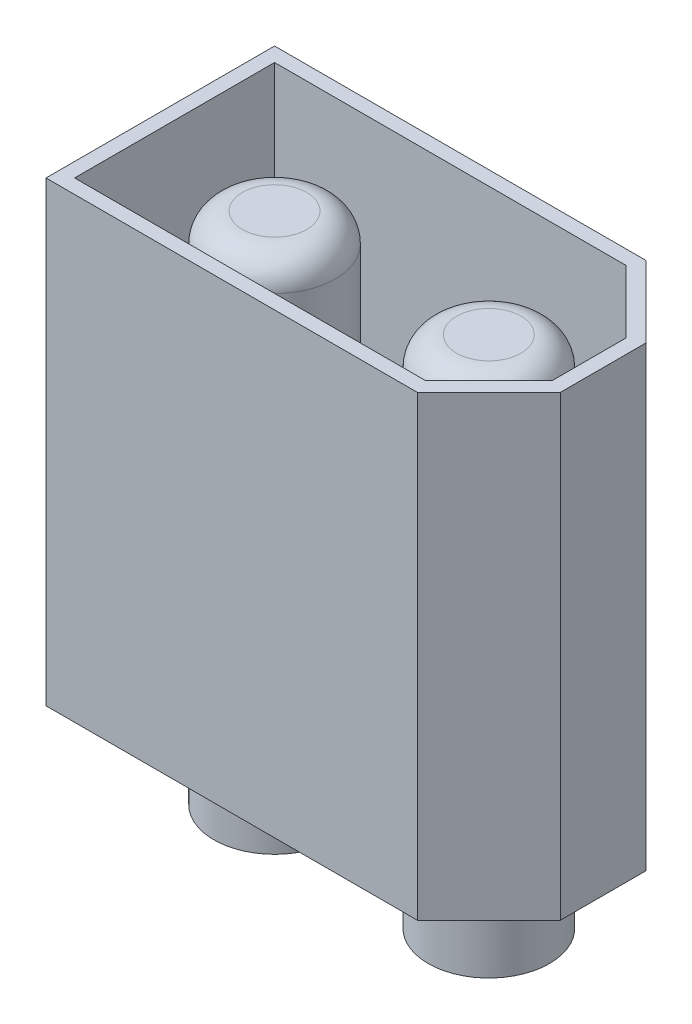
SolidWorks part; units mm, degrees
ref_plane "Front Plane" through (0, 0, 0) normal (0, 0, 1) x (1, 0, 0)
ref_plane "Top Plane" through (0, 0, 0) normal (0, 1, 0) x (1, 0, 0)
ref_plane "Right Plane" through (0, 0, 0) normal (1, 0, 0) x (0, 0, -1)
sketch "Sketch1" plane through (0, 0, 0) normal (0, 1, 0) x (1, 0, 0)
  line L0 (5.25, 4) -> (7.75, 1.5)
  line L1 (-7.75, 4) -> (7.75, 4)
  line L2 (-7.75, 4) -> (-7.75, -4)
  line L3 (-7.75, -4) -> (7.75, -4)
  line L4 (7.75, 4) -> (7.75, -4)
  line L5 (-7.75, 4) -> (7.75, -4) construction
  line L6 (-7.75, -4) -> (7.75, 4) construction
  line L7 (0, 0) -> (7.75, 0) construction
  line L8 (5.25, -4) -> (7.75, -1.5)
  point P0 (0, 0)
  dimension "D1" = 8
  dimension "D2" = 15.5
  dimension "D3" = 13
  dimension "D4" = 1.5
extrude "Boss-Extrude1" add sketch "Sketch1" along normal blind 16 contours L3 L8 L4 L0 L1 L2
shell "Shell1" thickness 0.5
sketch "Sketch2" plane through (0, 0, 0) normal (0, -1, 0) x (1, 0, 0)
  line L0 (0, 0) -> (0, 4) construction
  line L1 (-7.75, 4) -> (5.25, 4) construction
  circle A0 centre (-3.75, 0) radius 3
  circle A1 centre (3.75, 0) radius 3
  point P9 (0, 0)
  dimension "D1" = 6
  dimension "D2" = 3.75
extrude "Cut-Extrude1" cut sketch "Sketch2" against normal blind 1.5
sketch "Sketch3" plane through (0, 1.5, 0) normal (0, -1, 0) x (1, 0, 0)
  circle A0 centre (-3.75, 0) radius 2.125
  circle A1 centre (3.75, 0) radius 2.125
  dimension "D1" = 4.25
  dimension "D2" = 4.25
extrude "Boss-Extrude2" add sketch "Sketch3" along normal blind 4.5
sketch "Sketch4" plane through (0, 7, 0) normal (0, 1, 0) x (1, 0, 0)
  circle A0 centre (-3.75, 0) radius 2.125
  circle A1 centre (3.75, 0) radius 2.125
  dimension "D1" = 4.25
  dimension "D2" = 4.25
extrude "Boss-Extrude3" add sketch "Sketch4" along normal offset from surface (8 mm away) 1 up to face at (1.681, 16, 0)
fillet "Fillet1" radius 1 2 edges at (3.75, 15, 2.125) (-3.75, 15, 2.125)
